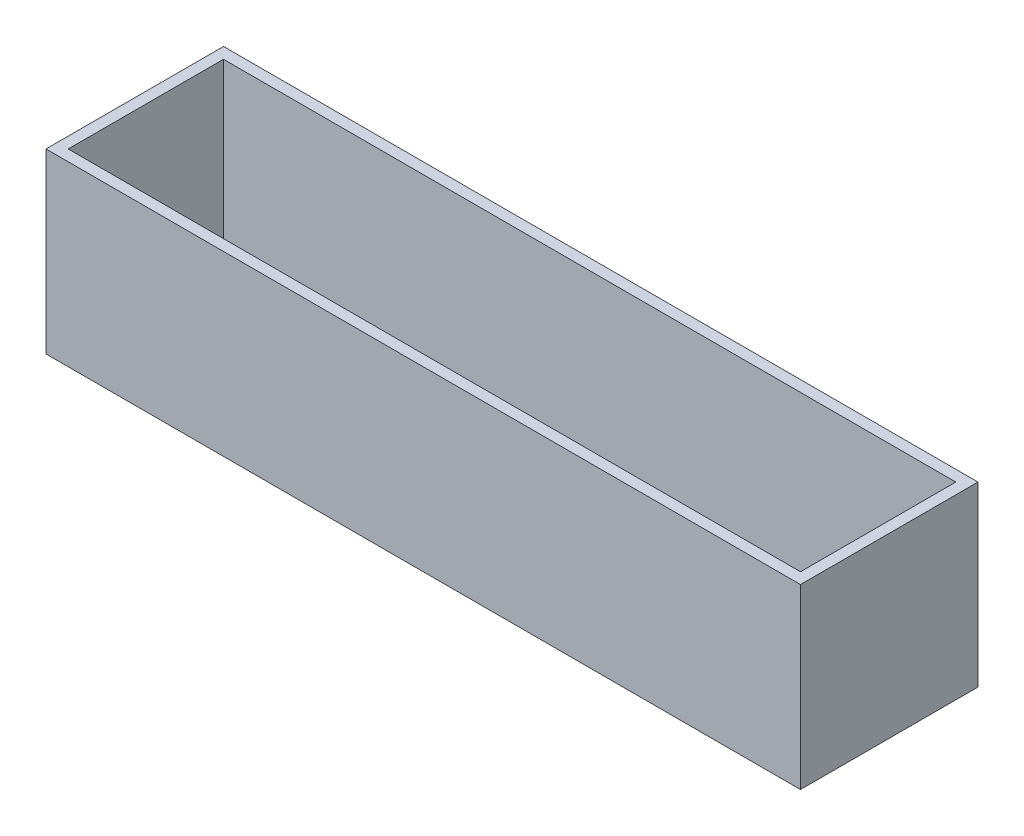
SolidWorks part; units mm, degrees
ref_plane "Alzado" through (0, 0, 0) normal (0, 0, 1) x (1, 0, 0)
ref_plane "Planta" through (0, 0, 0) normal (0, 1, 0) x (1, 0, 0)
ref_plane "Vista lateral" through (0, 0, 0) normal (1, 0, 0) x (0, 0, -1)
sketch "Croquis1" plane through (0, 0, 0) normal (0, 1, 0) x (1, 0, 0)
  line L1 (-81.573, 20.5618) -> (88.427, 20.5618)
  line L2 (-81.573, 20.5618) -> (-81.573, -19.4382)
  line L3 (-81.573, -19.4382) -> (88.427, -19.4382)
  line L4 (88.427, 20.5618) -> (88.427, -19.4382)
  dimension "D1" = 40
  dimension "D2" = 170
extrude "Saliente-Extruir1" add sketch "Croquis1" along normal blind 40
sketch "Croquis2" plane through (0, 40, 0) normal (0, 1, 0) x (1, 0, 0)
  line L0 (-81.573, 20.5618) -> (-81.573, -19.4382) construction
  line L1 (-79.073, 18.0618) -> (85.927, 18.0618)
  line L2 (-79.073, 18.0618) -> (-79.073, -16.9382)
  line L3 (-79.073, -16.9382) -> (85.927, -16.9382)
  line L4 (85.927, 18.0618) -> (85.927, -16.9382)
  line L5 (88.427, -19.4382) -> (88.427, 20.5618) construction
  line L6 (88.427, 20.5618) -> (-81.573, 20.5618) construction
  line L7 (-81.573, -19.4382) -> (88.427, -19.4382) construction
  dimension "D1" = 2.5
  dimension "D2" = 2.5
  dimension "D3" = 2.5
  dimension "D4" = 2.5
extrude "Cortar-Extruir1" cut sketch "Croquis2" against normal blind 37.5
